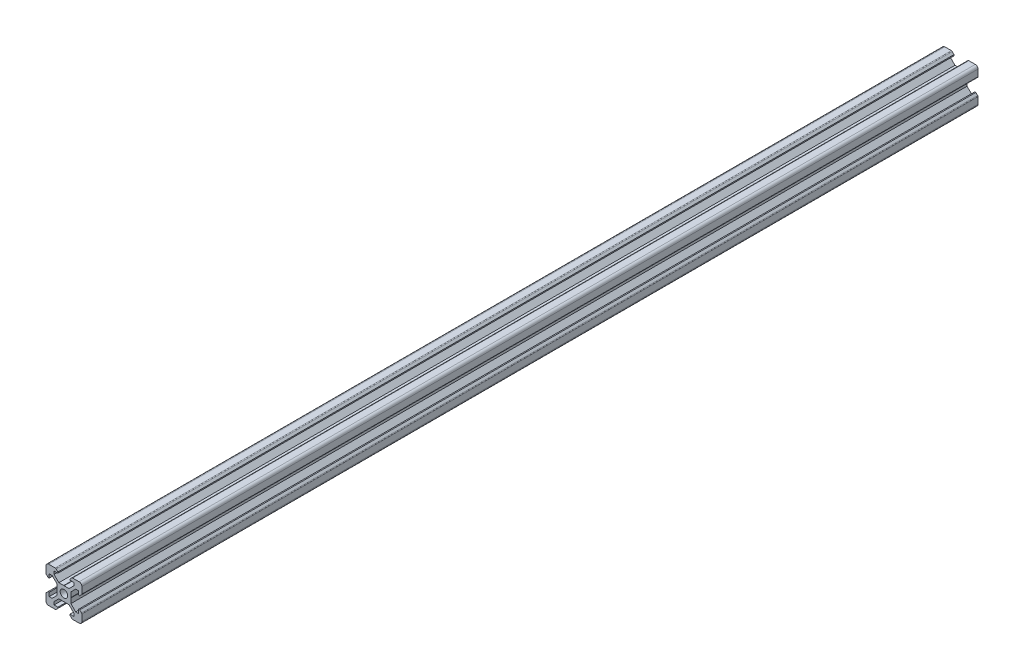
SolidWorks part; units mm, degrees
ref_plane "Front" through (0, 0, 0) normal (0, 0, 1) x (1, 0, 0)
ref_plane "Top" through (0, 0, 0) normal (0, 1, 0) x (1, 0, 0)
ref_plane "Right" through (0, 0, 0) normal (1, 0, 0) x (0, 0, -1)
sketch "Sketch1" plane through (0, 0, 0) normal (0, 0, 1) x (1, 0, 0)
  line L0 (-8.5, 10) -> (-10, 8.5) construction
  line L1 (-8.5, 10) -> (-4.8628, 10)
  line L2 (-10, 8.5) -> (-10, 4.8628)
  line L3 (-8.5, -10) -> (-4.8628, -10)
  line L4 (10, 8.5) -> (10, 4.8628)
  line L5 (-10, 10) -> (10, -10) construction
  line L6 (-10, -10) -> (10, 10) construction
  line L7 (-5.5, -8.2) -> (-3.3865, -8.2)
  line L8 (-8.2, -5.5) -> (-8.2, -3.3865)
  line L9 (-5.5, 8.2) -> (-3.3865, 8.2)
  line L10 (8.2, -5.5) -> (8.2, -3.3865)
  line L11 (-3.9005, 2.8395) -> (-6.561, 5.5)
  line L12 (-6.561, 5.5) -> (-8.2, 5.5)
  line L13 (-2.8395, -3.9005) -> (-0.1, -3.9005)
  line L14 (-3.9005, -2.8395) -> (-3.9005, -0.1)
  line L15 (-2.8395, 3.9005) -> (-0.1, 3.9005)
  line L16 (3.9005, -2.8395) -> (3.9005, -0.1)
  line L17 (-8.2, 3.3865) -> (-8.81, 3.3865)
  line L18 (-8.81, 3.3865) -> (-9.7976, 4.3741)
  line L19 (8.5, 10) -> (10, 8.5) construction
  line L20 (-2.8395, 3.9005) -> (-5.5, 6.561)
  line L21 (-5.5, 6.561) -> (-5.5, 8.2)
  line L22 (-3.3865, 8.2) -> (-3.3865, 8.81)
  line L23 (-3.3865, 8.81) -> (-4.3741, 9.7976)
  line L24 (0, 24.069) -> (0, -33.8154) construction
  line L25 (3.3865, 8.81) -> (4.3741, 9.7976)
  line L26 (3.3865, 8.2) -> (3.3865, 8.81)
  line L27 (5.5, 6.561) -> (5.5, 8.2)
  line L28 (2.8395, 3.9005) -> (5.5, 6.561)
  line L29 (3.3865, 8.2) -> (5.5, 8.2)
  line L30 (4.8628, 10) -> (8.5, 10)
  line L31 (-0.1, 3.9005) -> (0, 3.8005)
  line L32 (0.1, 3.9005) -> (0, 3.8005)
  line L33 (0.1, 3.9005) -> (2.8395, 3.9005)
  line L34 (25.9287, 0) -> (-28.3459, 0) construction
  line L35 (-0.1, -3.9005) -> (0, -3.8005)
  line L36 (0.1, -3.9005) -> (0, -3.8005)
  line L37 (0.1, -3.9005) -> (2.8395, -3.9005)
  line L38 (-3.9005, 0.1) -> (-3.8005, 0)
  line L39 (-3.8005, 0) -> (-3.9005, -0.1)
  line L40 (-3.9005, 0.1) -> (-3.9005, 2.8395)
  line L41 (3.9005, 0.1) -> (3.8005, 0)
  line L42 (3.8005, 0) -> (3.9005, -0.1)
  line L43 (3.9005, 0.1) -> (3.9005, 2.8395)
  line L44 (8.81, 3.3865) -> (9.7976, 4.3741)
  line L45 (8.2, 3.3865) -> (8.81, 3.3865)
  line L46 (6.561, 5.5) -> (8.2, 5.5)
  line L47 (3.9005, 2.8395) -> (6.561, 5.5)
  line L48 (2.8395, -3.9005) -> (5.5, -6.561)
  line L49 (3.9005, -2.8395) -> (6.561, -5.5)
  line L50 (-2.8395, -3.9005) -> (-5.5, -6.561)
  line L51 (-3.9005, -2.8395) -> (-6.561, -5.5)
  line L52 (6.561, -5.5) -> (8.2, -5.5)
  line L53 (-6.561, -5.5) -> (-8.2, -5.5)
  line L54 (-8.81, -3.3865) -> (-9.7976, -4.3741)
  line L55 (-8.2, -3.3865) -> (-8.81, -3.3865)
  line L56 (8.81, -3.3865) -> (9.7976, -4.3741)
  line L57 (8.2, -3.3865) -> (8.81, -3.3865)
  line L58 (8.2, 3.3865) -> (8.2, 5.5)
  line L59 (10, -4.8628) -> (10, -8.5)
  line L60 (-8.2, 3.3865) -> (-8.2, 5.5)
  line L61 (-10, -4.8628) -> (-10, -8.5)
  line L62 (-3.3865, -8.81) -> (-4.3741, -9.7976)
  line L63 (-3.3865, -8.2) -> (-3.3865, -8.81)
  line L64 (3.3865, -8.81) -> (4.3741, -9.7976)
  line L65 (3.3865, -8.2) -> (3.3865, -8.81)
  line L66 (-5.5, -6.561) -> (-5.5, -8.2)
  line L67 (5.5, -6.561) -> (5.5, -8.2)
  line L68 (3.3865, -8.2) -> (5.5, -8.2)
  line L69 (4.8628, -10) -> (8.5, -10)
  circle A0 centre (0, 0) radius 2.1
  arc A1 (-8.5, 10) -> (-10, 8.5) centre (-8.5, 8.5) ccw
  arc A2 (10, 8.5) -> (8.5, 10) centre (8.5, 8.5) ccw
  arc A3 (-4.3741, 9.7976) -> (-4.8628, 10) centre (-4.8628, 9.3088) ccw
  arc A4 (4.8628, 10) -> (4.3741, 9.7976) centre (4.8628, 9.3088) ccw
  arc A5 (-8.5, -10) -> (-10, -8.5) centre (-8.5, -8.5) cw
  arc A6 (9.7976, 4.3741) -> (10, 4.8628) centre (9.3088, 4.8628) ccw
  arc A7 (-10, 4.8628) -> (-9.7976, 4.3741) centre (-9.3088, 4.8628) ccw
  arc A8 (-10, -4.8628) -> (-9.7976, -4.3741) centre (-9.3088, -4.8628) cw
  arc A9 (9.7976, -4.3741) -> (10, -4.8628) centre (9.3088, -4.8628) cw
  arc A10 (10, -8.5) -> (8.5, -10) centre (8.5, -8.5) cw
  arc A11 (-4.3741, -9.7976) -> (-4.8628, -10) centre (-4.8628, -9.3088) cw
  arc A12 (4.8628, -10) -> (4.3741, -9.7976) centre (4.8628, -9.3088) cw
  point P17 (-9.25, 9.25)
  point P21 (9.25, 9.25)
  dimension "D2" = 4.2
  dimension "D4" = 1.5
  dimension "D3" = 20
  dimension "D5" = 0.529
  dimension "D6" = 6.773
  dimension "D7" = 90
  dimension "D8" = 11
  dimension "D9" = 0.61
  dimension "D10" = 0.1
  dimension "D11" = 0.1
  dimension "D12" = 0.1
  dimension "D13" = 0.1
  dimension "D14" = 5.679
  dimension "D15" = 1.639
  dimension "D16" = 1.8
  dimension "D17" = 90
  dimension "D18" = 6.773
  dimension "D19" = 90
extrude "Boss-Extrude1" add sketch "Sketch1" along normal blind 500
